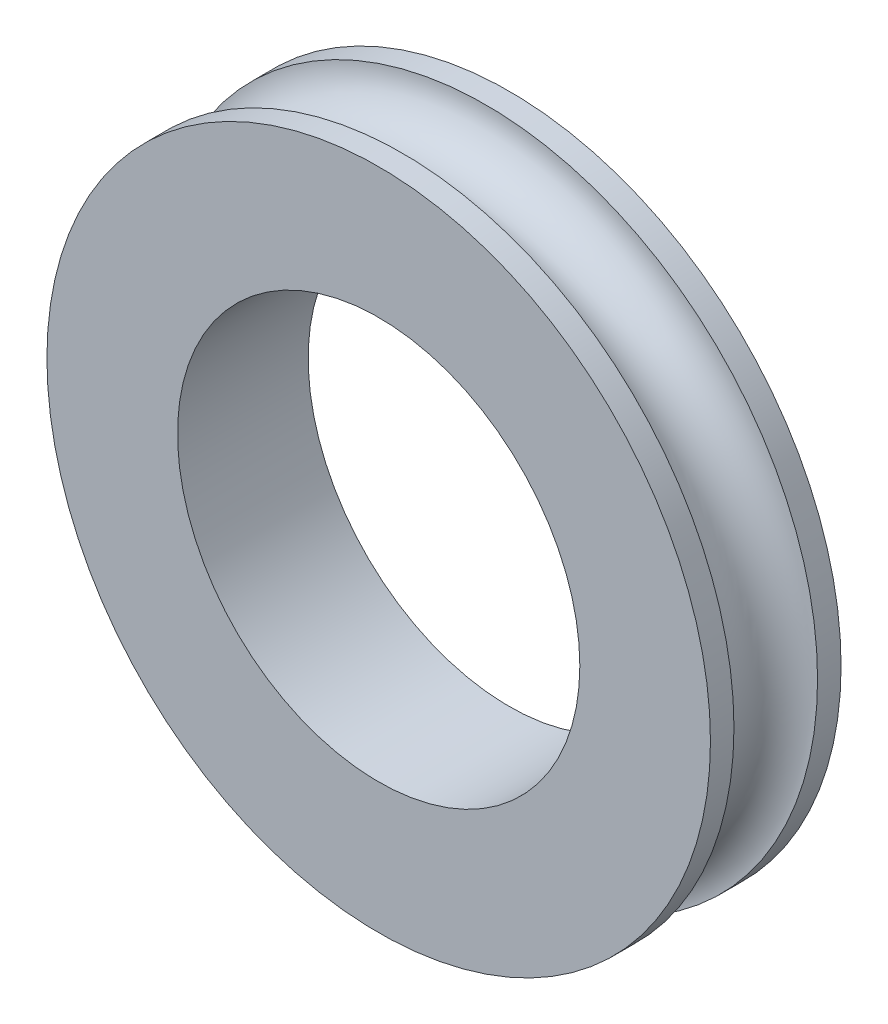
SolidWorks part; units mm, degrees
ref_plane "Front Plane" through (0, 0, 0) normal (0, 0, 1) x (1, 0, 0)
ref_plane "Top Plane" through (0, 0, 0) normal (0, 1, 0) x (1, 0, 0)
ref_plane "Right Plane" through (0, 0, 0) normal (1, 0, 0) x (0, 0, -1)
sketch "Sketch1" plane through (0, 0, 0) normal (1, 0, 0) x (0, 0, -1)
  line L0 (0, 3.85) -> (2.5, 3.85)
  line L1 (2.5, 3.85) -> (2.5, 6.35)
  line L2 (2.5, 6.35) -> (2.05, 6.35)
  line L3 (0.45, 6.35) -> (0, 6.35)
  line L4 (0, 6.35) -> (0, 3.85)
  line L6 (0, 0) -> (2.5, 0) construction
  arc A0 (2.05, 6.35) -> (0.45, 6.35) centre (1.25, 6.35) cw
  dimension "D3" = 0.8
  dimension "D1" = 3.85
  dimension "D2" = 2.5
revolve "Revolve1" add sketch "Sketch1" angle 360 about L6
